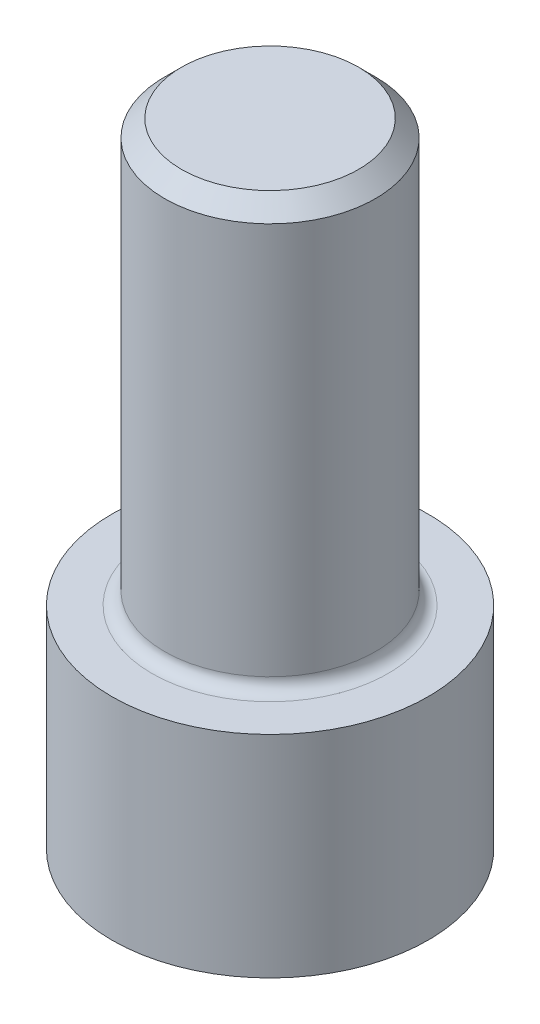
SolidWorks part; units mm, degrees
ref_plane "Front Plane" through (0, 0, 0) normal (0, 0, 1) x (1, 0, 0)
ref_plane "Top Plane" through (0, 0, 0) normal (0, 1, 0) x (1, 0, 0)
ref_plane "Right Plane" through (0, 0, 0) normal (1, 0, 0) x (0, 0, -1)
sketch "Sketch2" plane through (0, 0, 0) normal (0, 1, 0) x (1, 0, 0)
  circle A0 centre (0, 0) radius 4.7625
extrude "Boss-Extrude1" add sketch "Sketch2" along normal blind 6.35
sketch "Sketch3" plane through (0, 0, 0) normal (0, -1, 0) x (1, 0, 0)
  line L1 (2.54, 0) -> (1.27, 2.1997)
  line L2 (1.27, 2.1997) -> (-1.27, 2.1997)
  line L3 (-1.27, 2.1997) -> (-2.54, 0)
  line L4 (-2.54, 0) -> (-1.27, -2.1997)
  line L5 (-1.27, -2.1997) -> (1.27, -2.1997)
  line L6 (1.27, -2.1997) -> (2.54, 0)
  circle A0 centre (0, 0) radius 2.54 construction
extrude "Cut-Extrude1" cut sketch "Sketch3" against normal blind 3.81
sketch "Sketch4" plane through (0, 6.35, 0) normal (0, 1, 0) x (1, 0, 0)
  circle A0 centre (0, 0) radius 3.175
extrude "Boss-Extrude5" add sketch "Sketch4" along normal blind 12.7
fillet "Fillet2" radius 0.381 1 edges at (0, 6.35, 3.175)
chamfer "Chamfer1" distance 0.508 angle 45 1 edges at (0, 19.05, 3.175)
